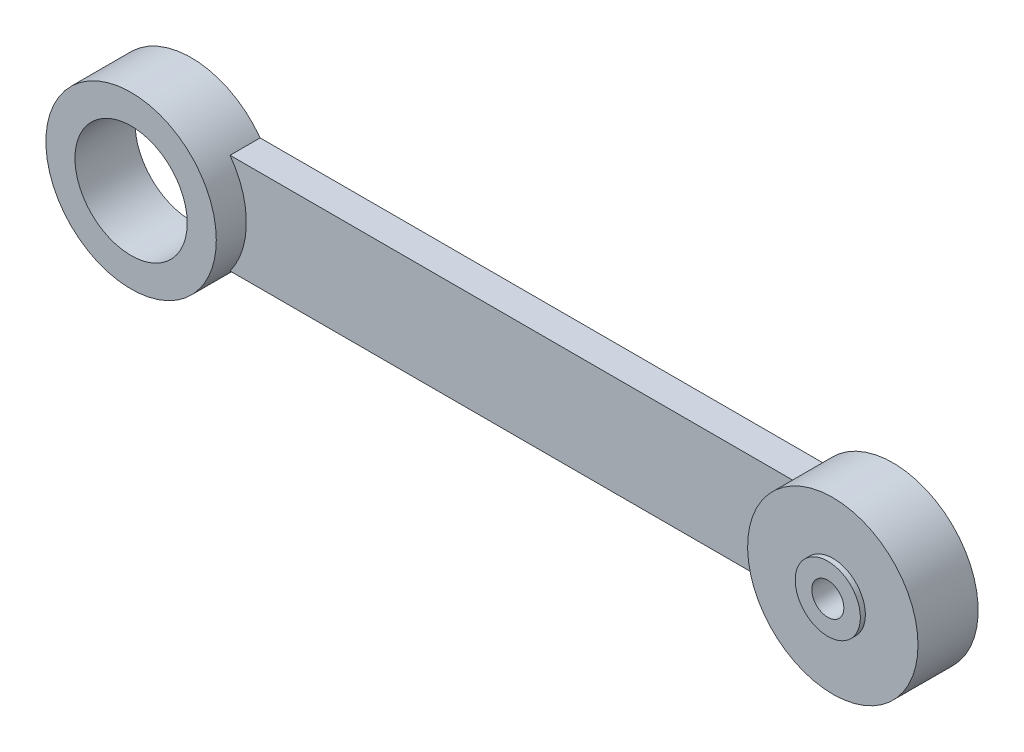
SolidWorks part; units mm, degrees
ref_plane "Front Plane" through (0, 0, 0) normal (0, 0, 1) x (1, 0, 0)
ref_plane "Top Plane" through (0, 0, 0) normal (0, 1, 0) x (1, 0, 0)
ref_plane "Right Plane" through (0, 0, 0) normal (1, 0, 0) x (0, 0, -1)
sketch "Sketch1" plane through (0, 0, 0) normal (0, 0, 1) x (1, 0, 0)
  line L6 (0, 0) -> (70, 0) construction
  line L7 (0, 5) -> (70, 5) construction
  line L8 (6.8739, 5) -> (63.1261, 5)
  line L9 (6.8739, -5) -> (63.1261, -5)
  circle A4 centre (0, 0) radius 5.6
  circle A5 centre (0, 0) radius 8.5 construction
  circle A6 centre (70, 0) radius 8.5 construction
  arc A7 (6.8739, 5) -> (6.8739, -5) centre (0, 0) ccw
  arc A8 (63.1261, 5) -> (63.1261, -5) centre (70, 0) cw
  dimension "D4" = 17
  dimension "D5" = 5
  dimension "D2" = 11.2
  dimension "D3" = 17
  dimension "D1" = 70
extrude "Boss-Extrude1" add sketch "Sketch1" along normal blind 3
sketch "Sketch2" plane through (0, 0, 0) normal (0, 0, 1) x (1, 0, 0)
  circle A0 centre (0, 0) radius 8.5
  circle A1 centre (0, 0) radius 5.6
  dimension "D1" = 11.2
extrude "Boss-Extrude2" add sketch "Sketch2" along normal blind 6
sketch "Sketch3" plane through (0, 0, 0) normal (0, 0, 1) x (1, 0, 0)
  circle A0 centre (70, 0) radius 8.5
extrude "Boss-Extrude3" add sketch "Sketch3" along normal blind 6 from surface at 0 starting at face at (35, 0, 0)
sketch "Sketch4" plane through (0, 0, 0) normal (0, 0, 1) x (1, 0, 0)
  circle A0 centre (70, 0) radius 1.6
  dimension "D1" = 3.2
extrude "Cut-Extrude1" cut sketch "Sketch4" along normal through all
sketch "Sketch5" plane through (0, 0, 0) normal (0, 0, 1) x (1, 0, 0)
  circle A0 centre (70, 0) radius 3.3
extrude "Cut-Extrude2" cut sketch "Sketch5" along normal blind 1.5
sketch "Sketch6" plane through (0, 0, 0) normal (0, 0, 1) x (1, 0, 0)
  circle A0 centre (70, 0) radius 1.6
  circle A1 centre (70, 0) radius 3.25
  dimension "D1" = 6.5
extrude "Boss-Extrude4" add sketch "Sketch6" along normal blind 0.5 from surface at 6 starting at face at (71.6, 0, 6)
